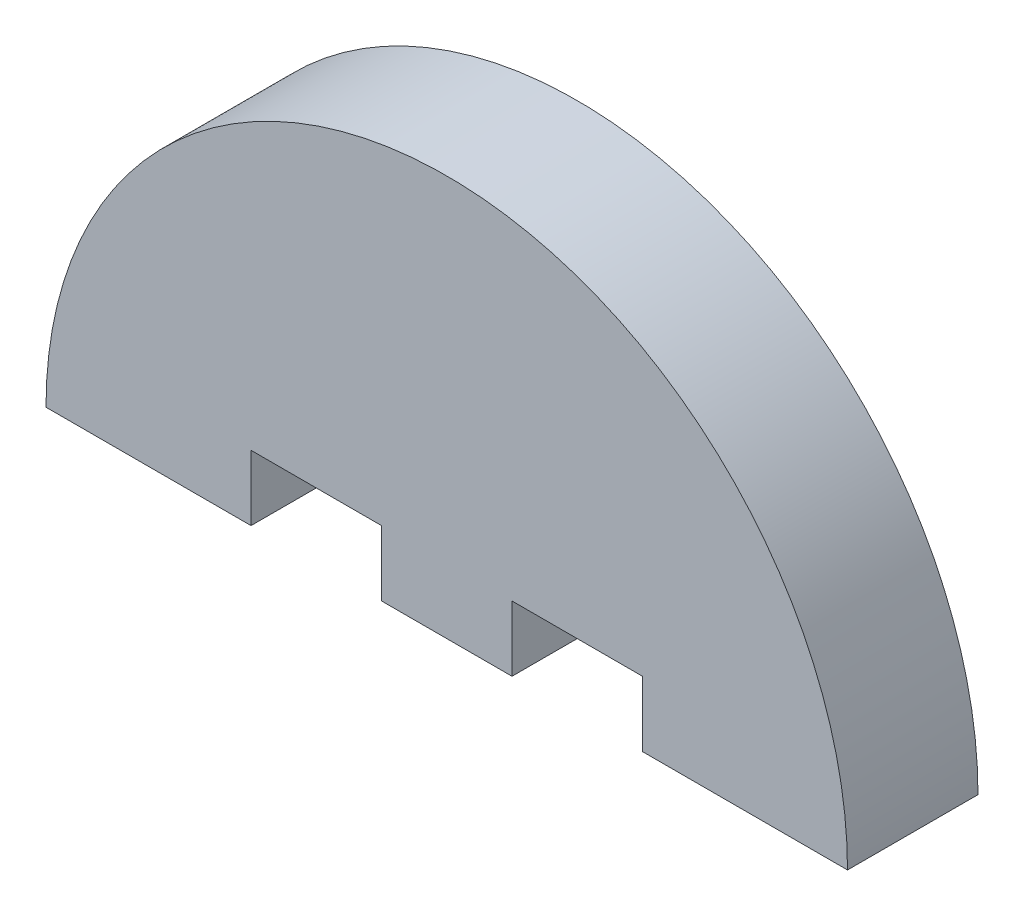
SolidWorks part; units mm, degrees
ref_plane "Front Plane" through (0, 0, 0) normal (0, 0, 1) x (1, 0, 0)
ref_plane "Top Plane" through (0, 0, 0) normal (0, 1, 0) x (1, 0, 0)
ref_plane "Right Plane" through (0, 0, 0) normal (1, 0, 0) x (0, 0, -1)
sketch "Model" plane through (0, 0, 0) normal (0, 0, 1) x (1, 0, 0)
  line L0 (3624.683, 1289.903) -> (3615.2545, 1289.903)
  line L1 (3609.2545, 1289.903) -> (3603.2545, 1289.903)
  line L2 (3597.2545, 1289.903) -> (3587.8259, 1289.903)
  line L3 (3615.2545, 1292.903) -> (3615.2545, 1289.903)
  line L4 (3615.2545, 1292.903) -> (3609.2545, 1292.903)
  line L5 (3609.2545, 1292.903) -> (3609.2545, 1289.903)
  line L6 (3597.2545, 1292.903) -> (3597.2545, 1289.903)
  line L7 (3597.2545, 1292.903) -> (3603.2545, 1292.903)
  line L8 (3603.2545, 1292.903) -> (3603.2545, 1289.903)
  arc A0 (3624.683, 1289.903) -> (3587.8259, 1289.903) centre (3606.2545, 1289.903) ccw
extrude "Boss-Extrude1" add sketch "Model" along normal blind 6 contours A0 L2 L6 L7 L8 L1 L5 L4 L3 L0
